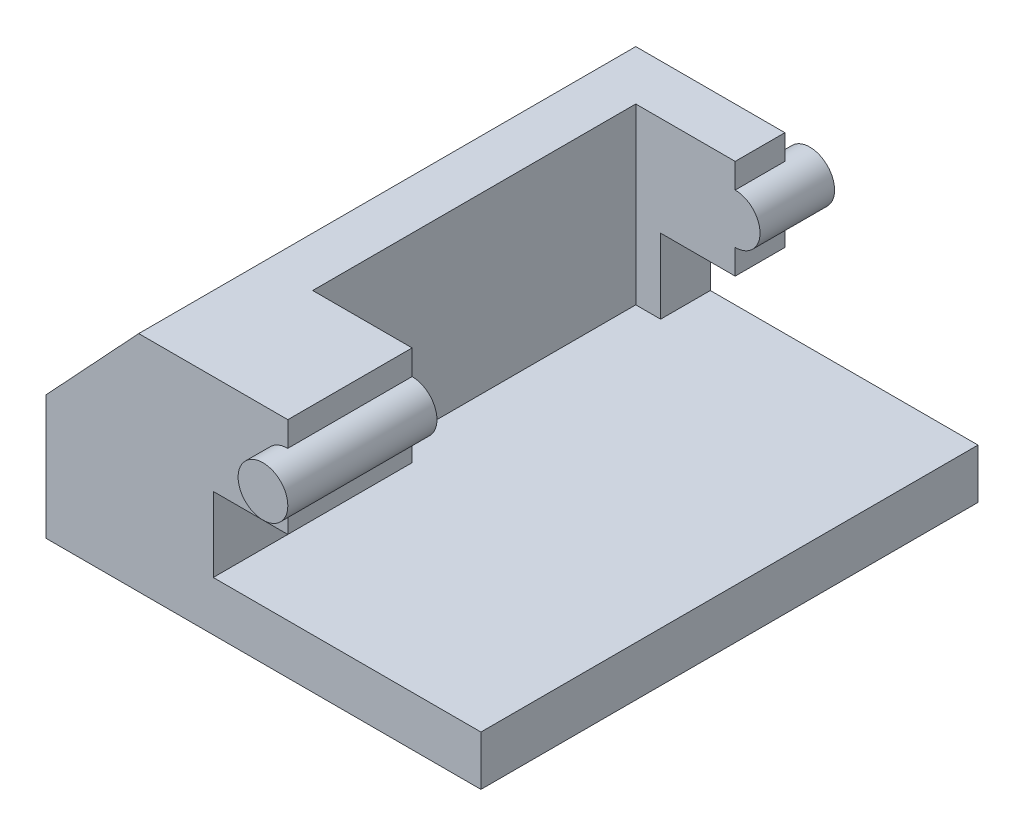
SolidWorks part; units mm, degrees
material "Plain Carbon Steel"
ref_plane "Front Plane" through (0, 0, 0) normal (0, 0, 1) x (1, 0, 0)
ref_plane "Top Plane" through (0, 0, 0) normal (0, 1, 0) x (1, 0, 0)
ref_plane "Right Plane" through (0, 0, 0) normal (1, 0, 0) x (0, 0, -1)
sketch "Sketch3" plane through (0, 0, 0) normal (0, 0, 1) x (1, 0, 0)
  line L0 (0, 0) -> (-87.5, 0)
  line L1 (-87.5, 0) -> (-87.5, 25)
  line L2 (-87.5, 25) -> (-68.8497, 45)
  line L3 (-68.8497, 45) -> (-38.8497, 45)
  line L5 (-38.8497, 45) -> (-38.8497, 40)
  line L6 (-38.8497, 25) -> (-53.8497, 25)
  line L7 (-53.8497, 25) -> (-53.8497, 10)
  line L8 (-53.8497, 10) -> (0, 10)
  line L9 (0, 10) -> (0, 0)
  line L10 (-38.8497, 30) -> (-38.8497, 25)
  circle A1 centre (-38.8497, 35) radius 5
  point P11 (0, 0)
  dimension "D1" = 10
  dimension "D2" = 20
  dimension "D3" = 10
  dimension "D4" = 10
  dimension "D5" = 15
  dimension "D6" = 87.5
  dimension "D7" = 25
  dimension "D8" = 43
  dimension "D9" = 30
  dimension "D10" = 15
extrude "Boss-Extrude6" add sketch "Sketch3" along normal mid plane 100 contours A1 | A1 L5 L3 L2 L1 L0 L9 L8 L7 L6 L10
sketch "Sketch10" plane through (0, 0, 50) normal (0, 0, 1) x (1, 0, 0)
  circle A0 centre (-38.8497, 35) radius 5
  dimension "D1" = 10
extrude "Boss-Extrude7" add sketch "Sketch10" along normal blind 5
sketch "Sketch11" plane through (0, 0, -50) normal (0, 0, -1) x (-1, 0, 0)
  circle A0 centre (38.8497, 35) radius 5
extrude "Boss-Extrude8" add sketch "Sketch11" along normal blind 5
sketch "Sketch13" plane through (0, 0, 0) normal (0, 0, 1) x (1, 0, 0)
  line L1 (-58.8497, 56.596) -> (0, 56.596)
  line L2 (-58.8497, 56.596) -> (-58.8497, 10)
  line L3 (-58.8497, 10) -> (0, 10)
  line L4 (0, 56.596) -> (0, 10)
  dimension "D1" = 10
extrude "Cut-Extrude3" cut sketch "Sketch13" against normal offset from surface 10 and the other way blind 25 up to face at (-46.5407, 23.1818, -50)
